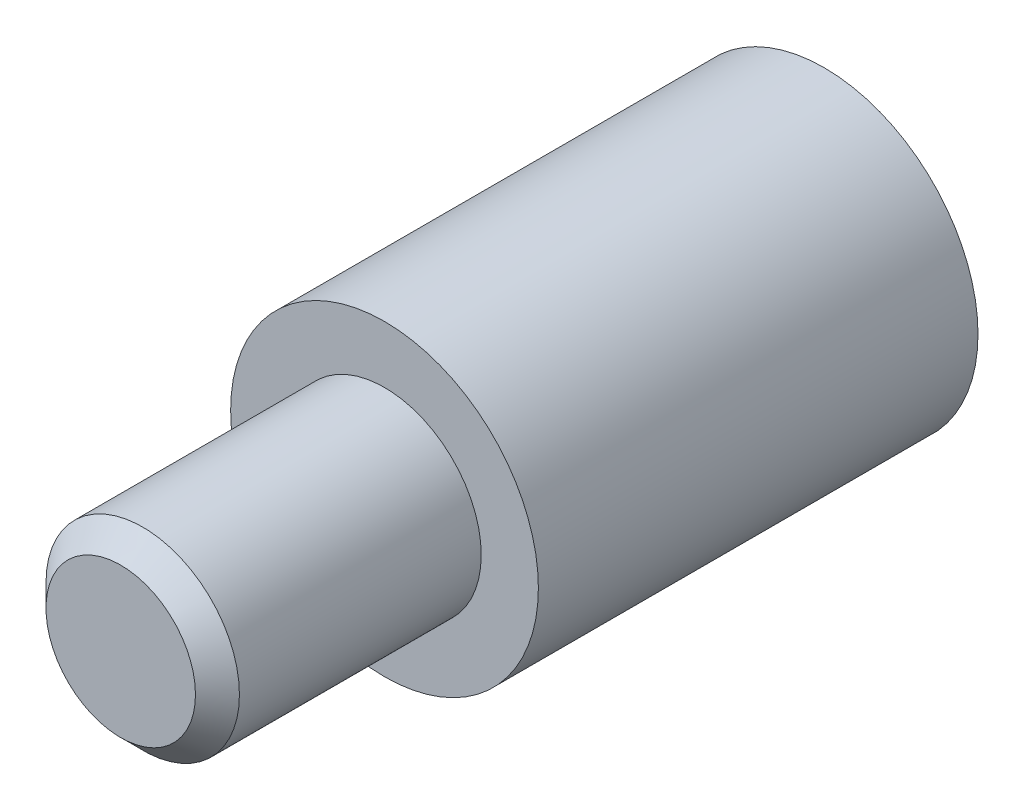
SolidWorks part; units mm, degrees
ref_plane "Front Plane" through (0, 0, 0) normal (0, 0, 1) x (1, 0, 0)
ref_plane "Top Plane" through (0, 0, 0) normal (0, 1, 0) x (1, 0, 0)
ref_plane "Right Plane" through (0, 0, 0) normal (1, 0, 0) x (0, 0, -1)
sketch "Sketch1" plane through (0, 0, 107.9354) normal (0, 0, -1) x (-1, 0, 0)
  circle A0 centre (-59.7974, 58.0158) radius 3.5
  dimension "D1" = 7
extrude "Boss-Extrude1" add sketch "Sketch1" along normal blind 7
sketch "Sketch2" plane through (0, 0, 100.9354) normal (0, 0, -1) x (-1, 0, 0)
  circle A0 centre (-59.7974, 58.0158) radius 3.5
  circle A1 centre (-59.7974, 58.0158) radius 2
  dimension "D1" = 4
extrude "Boss-Extrude2" add sketch "Sketch2" along normal blind 3
sketch "Sketch3" plane through (0, 0, 107.9354) normal (0, 0, 1) x (1, 0, 0)
  circle A0 centre (59.7974, 58.0158) radius 2.2
  circle A1 centre (59.7974, 58.0158) radius 2.5 construction
  dimension "D1" = 0.3
extrude "Boss-Extrude3" add sketch "Sketch3" along normal blind 6
chamfer "Chamfer1" distance 0.5 angle 45 1 edges at (61.9974, 58.0158, 113.9354)
